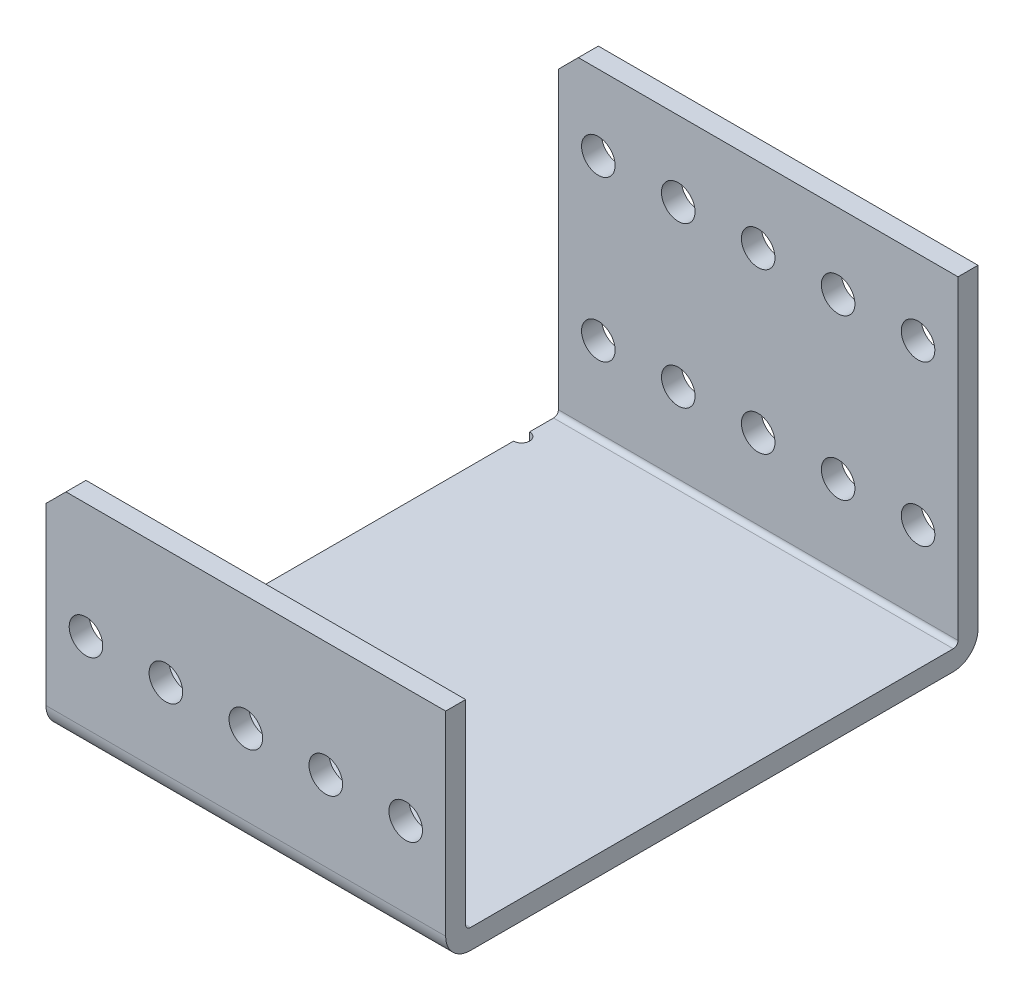
SolidWorks part; units mm, degrees
ref_plane "Front Plane" through (0, 0, 0) normal (0, 0, 1) x (1, 0, 0)
ref_plane "Top Plane" through (0, 0, 0) normal (0, 1, 0) x (1, 0, 0)
ref_plane "Right Plane" through (0, 0, 0) normal (1, 0, 0) x (0, 0, -1)
ref_plane "Plane4" through (0, 57.8164, 0) normal (0, 1, 0) x (1, 0, 0)
sketch "Sketch1" plane through (0, 57.8164, 0) normal (0, 1, 0) x (1, 0, 0)
  line L0 (602.398, -145.5605) -> (602.398, -60.9785)
  line L1 (602.398, -60.9785) -> (-96.102, -60.9785)
  line L2 (-96.102, -60.9785) -> (-96.102, -145.5605)
  line L3 (-96.102, -145.5605) -> (602.398, -145.5605)
  dimension "D1" = 698.5
extrude "Boss-Extrude1" add sketch "Sketch1" against normal blind 34.925
sketch "Sketch2" plane through (602.398, 0, 0) normal (1, 0, 0) x (0, 0, -1)
  line L0 (-60.9785, 57.8164) -> (-142.3855, 57.8164)
  line L1 (-142.3855, 57.8164) -> (-142.3855, 26.0664)
  line L2 (-142.3855, 26.0664) -> (-60.9785, 26.0664)
  line L3 (-60.9785, 26.0664) -> (-60.9785, 57.8164)
extrude "Cut-Extrude1" cut sketch "Sketch2" against normal through all
sketch "Sketch3" plane through (0, 26.0664, 0) normal (0, 1, 0) x (-1, 0, 0)
  line L0 (96.102, 60.9785) -> (-602.398, 60.9785)
  line L1 (-602.398, 60.9785) -> (-602.398, 64.1535)
  line L2 (-602.398, 64.1535) -> (96.102, 64.1535)
  line L3 (96.102, 64.1535) -> (96.102, 60.9785)
  line L5 (-602.398, 142.3855) -> (-602.398, 60.9785) construction
  line L6 (96.102, 142.3855) -> (96.102, 60.9785) construction
extrude "Boss-Extrude2" add sketch "Sketch3" along normal blind 50.8
hole_wizard "M2 Clearance Hole1" positions "Sketch5" profile "Sketch4" hole size "M2" standard "ANSI Metric" end condition through all
sketch "Sketch5" plane through (0, 26.0664, 0) normal (0, 1, 0) x (1, 0, 0)
  point P0 (-96.102, -136.5435)
  point P1 (-96.102, -69.9955)
sketch "Sketch4" plane through (-96.102, 26.0664, 136.5435) normal (1, 0, 0) x (0, 0, 1)
  line L0 (0, 0) -> (0, 3.175)
  line L1 (0, 3.175) -> (1.27, 3.175)
  line L2 (1.27, 3.175) -> (1.27, 0)
  line L5 (1.27, 0) -> (0, 0)
  line L11 (0, -6.35) -> (0, 107.95) construction
  dimension "Thru Hole Dia." = 2.54
  dimension "Thru Hole Depth" = 3.175
hole_wizard "M5 Clearance Hole1" positions "Sketch7" profile "Sketch6" hole size "M5" standard "ANSI Metric" end condition through all
sketch "Sketch7" plane through (0, 0, 60.9785) normal (0, 0, -1) x (-1, 0, 0)
  point P0 (-469.048, 64.9284)
  point P1 (-481.748, 64.9284)
  point P2 (-469.048, 39.5284)
  point P3 (-481.748, 39.5284)
  point P4 (-456.348, 39.5284)
  point P5 (-443.648, 39.5284)
  point P6 (-430.948, 39.5284)
  point P7 (-418.248, 39.5284)
  point P8 (-405.548, 39.5284)
  point P9 (-392.848, 39.5284)
  point P10 (-380.148, 39.5284)
  point P11 (-367.448, 39.5284)
  point P12 (-354.748, 39.5284)
  point P13 (-342.048, 39.5284)
  point P14 (-329.348, 39.5284)
  point P15 (-316.648, 39.5284)
  point P16 (-303.948, 39.5284)
  point P17 (-291.248, 39.5284)
  point P18 (-278.548, 39.5284)
  point P19 (-265.848, 39.5284)
  point P20 (-253.148, 39.5284)
  point P21 (-240.448, 39.5284)
  point P22 (-227.748, 39.5284)
  point P23 (-215.048, 39.5284)
  point P24 (-202.348, 39.5284)
  point P25 (-189.648, 39.5284)
  point P26 (-176.948, 39.5284)
  point P27 (-164.248, 39.5284)
  point P28 (-151.548, 39.5284)
  point P29 (-138.848, 39.5284)
  point P30 (-126.148, 39.5284)
  point P31 (-113.448, 39.5284)
  point P32 (-100.748, 39.5284)
  point P33 (-88.048, 39.5284)
  point P34 (-75.348, 39.5284)
  point P35 (-62.648, 39.5284)
  point P36 (-49.948, 39.5284)
  point P37 (-37.248, 39.5284)
  point P38 (-24.548, 39.5284)
  point P39 (-11.848, 39.5284)
  point P40 (0.852, 39.5284)
  point P41 (13.552, 39.5284)
  point P42 (26.252, 39.5284)
  point P43 (38.952, 39.5284)
  point P44 (51.652, 39.5284)
  point P45 (64.352, 39.5284)
  point P46 (77.052, 39.5284)
  point P47 (89.752, 39.5284)
  point P48 (-456.348, 64.9284)
  point P49 (-443.648, 64.9284)
  point P50 (-430.948, 64.9284)
  point P51 (-418.248, 64.9284)
  point P52 (-405.548, 64.9284)
  point P53 (-392.848, 64.9284)
  point P54 (-380.148, 64.9284)
  point P55 (-367.448, 64.9284)
  point P56 (-354.748, 64.9284)
  point P57 (-342.048, 64.9284)
  point P58 (-329.348, 64.9284)
  point P59 (-316.648, 64.9284)
  point P60 (-303.948, 64.9284)
  point P61 (-291.248, 64.9284)
  point P62 (-278.548, 64.9284)
  point P63 (-265.848, 64.9284)
  point P64 (-253.148, 64.9284)
  point P65 (-240.448, 64.9284)
  point P66 (-227.748, 64.9284)
  point P67 (-215.048, 64.9284)
  point P68 (-202.348, 64.9284)
  point P69 (-189.648, 64.9284)
  point P70 (-176.948, 64.9284)
  point P71 (-164.248, 64.9284)
  point P72 (-151.548, 64.9284)
  point P73 (-138.848, 64.9284)
  point P74 (-126.148, 64.9284)
  point P75 (-113.448, 64.9284)
  point P76 (-100.748, 64.9284)
  point P77 (-88.048, 64.9284)
  point P78 (-75.348, 64.9284)
  point P79 (-62.648, 64.9284)
  point P80 (-49.948, 64.9284)
  point P81 (-37.248, 64.9284)
  point P82 (-24.548, 64.9284)
  point P83 (-11.848, 64.9284)
  point P84 (0.852, 64.9284)
  point P85 (13.552, 64.9284)
  point P86 (26.252, 64.9284)
  point P87 (38.952, 64.9284)
  point P88 (51.652, 64.9284)
  point P89 (64.352, 64.9284)
  point P90 (77.052, 64.9284)
  point P91 (89.752, 64.9284)
  point P97 (-494.448, 64.9284)
  point P98 (-494.448, 39.5284)
  point P99 (-507.148, 64.9284)
  point P100 (-507.148, 39.5284)
  point P101 (-519.848, 64.9284)
  point P102 (-519.848, 39.5284)
  point P103 (-532.548, 64.9284)
  point P104 (-532.548, 39.5284)
  point P105 (-545.248, 64.9284)
  point P106 (-545.248, 39.5284)
  point P107 (-557.948, 64.9284)
  point P108 (-557.948, 39.5284)
  point P109 (-570.648, 64.9284)
  point P110 (-570.648, 39.5284)
  point P111 (-583.348, 64.9284)
  point P112 (-583.348, 39.5284)
  point P113 (-596.048, 64.9284)
  point P114 (-596.048, 39.5284)
  dimension "D1" = 10
sketch "Sketch6" plane through (469.048, 64.9284, 60.9785) normal (1, 0, 0) x (0, 1, 0)
  line L0 (0, 0) -> (0, 84.582)
  line L1 (0, 84.582) -> (2.667, 84.582)
  line L2 (2.667, 84.582) -> (2.667, 0)
  line L5 (2.667, 0) -> (0, 0)
  line L11 (0, -6.35) -> (0, 107.95) construction
  dimension "Thru Hole Dia." = 5.334
  dimension "Thru Hole Depth" = 84.582
chamfer "Chamfer1" distance 3.175 angle 45 4 edges at (-96.102, 57.8164, 143.973) (-96.102, 76.8664, 62.566) (602.398, 76.8664, 62.566) (602.398, 57.8164, 143.973)
fillet "Fillet1" radius 0.762 2 edges at (253.148, 26.0664, 64.1535) (253.148, 26.0664, 142.3855)
fillet "Fillet2" radius 3.937 2 edges at (253.148, 22.8914, 145.5605) (253.148, 22.8914, 60.9785)
sketch "Sketch8" plane through (0, 0, 60.9785) normal (0, 0, -1) x (-1, 0, 0)
  line L1 (-693.323, 170.3588) -> (32.602, 170.3588)
  line L2 (-693.323, 170.3588) -> (-693.323, -47.8575)
  line L3 (-693.323, -47.8575) -> (32.602, -47.8575)
  line L4 (32.602, 170.3588) -> (32.602, -47.8575)
  line L5 (-693.323, 170.3588) -> (32.602, -47.8575) construction
  line L6 (-693.323, -47.8575) -> (32.602, 170.3588) construction
  line L7 (38.952, 39.5284) -> (26.252, 39.5284) construction
  point P4 (-330.3605, 61.2506)
  point P5 (32.602, 39.5284)
extrude "Cut-Extrude2" cut sketch "Sketch8" against normal through all
